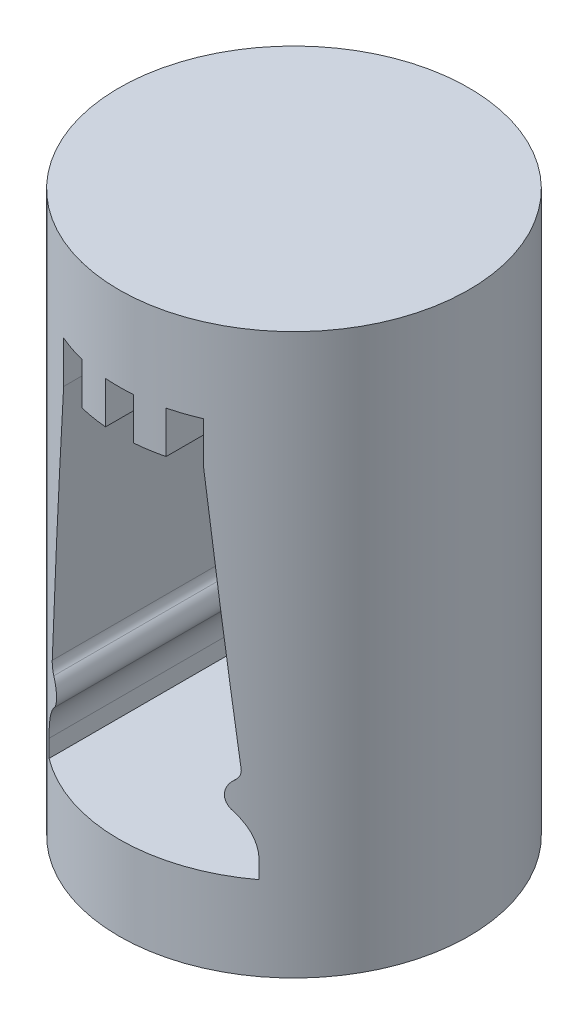
SolidWorks part; units mm, degrees
ref_plane "Front" through (0, 0, 0) normal (0, 0, 1) x (1, 0, 0)
ref_plane "Top" through (0, 0, 0) normal (0, 1, 0) x (1, 0, 0)
ref_plane "Right" through (0, 0, 0) normal (1, 0, 0) x (0, 0, -1)
sketch "Sketch2" plane through (0, 0, 0) normal (0, 1, 0) x (1, 0, 0)
  circle A0 centre (0, 0) radius 12.5
  dimension "D1" = 25
extrude "Boss-Extrude1" add sketch "Sketch2" along normal mid plane 40
sketch "Sketch3" plane through (0, 0, 0) normal (0, 0, 1) x (1, 0, 0)
  line L0 (-7.5, -14) -> (7.5, -14)
  line L2 (-7.5, -12.75) -> (-7.5, -14)
  line L3 (0, -50) -> (0, 50) construction
  line L5 (-5, 11) -> (-5, 14)
  line L6 (-5, 14) -> (-3, 14)
  line L7 (-3, 14) -> (-3, 11)
  line L8 (-3, 11) -> (-1, 11)
  line L9 (-1, 11) -> (-1, 14)
  line L17 (1, 11) -> (1, 14)
  line L18 (3, 11) -> (1, 11)
  line L19 (3, 14) -> (3, 11)
  line L20 (5, 14) -> (3, 14)
  line L21 (5, 11) -> (5, 14)
  line L23 (7.5, -12.75) -> (7.5, -14)
  line L24 (-1, 14) -> (1, 14)
  line L25 (-6.7499, -7.2906) -> (-5, 11)
  line L26 (6.7499, -7.2906) -> (5, 11)
  arc A4 (-6.3554, -9.8931) -> (-7.5, -12.75) centre (-3.3622, -12.75) ccw
  arc A6 (-6.456, -8.0123) -> (-6.3554, -9.8931) centre (-7.2911, -9) cw
  arc A13 (6.456, -8.0123) -> (6.3554, -9.8931) centre (7.2911, -9) ccw
  arc A14 (6.3554, -9.8931) -> (7.5, -12.75) centre (3.3622, -12.75) cw
  arc A15 (-6.456, -8.0123) -> (-6.7499, -7.2906) centre (-5.9135, -7.3706) cw
  arc A17 (6.456, -8.0123) -> (6.7499, -7.2906) centre (5.9135, -7.3706) ccw
  point P0 (0, -14)
  dimension "D1" = 14
  dimension "D6" = 1.25
  dimension "D7" = 5
  dimension "D2" = 15
  dimension "D3" = 14
  dimension "D4" = 3
  dimension "D5" = 2
extrude "Cut-Extrude1" cut sketch "Sketch3" against normal through all both and the other way through all
sketch "Sketch4" plane through (0, -20, 0) normal (0, -1, 0) x (-1, 0, 0)
  circle A0 centre (0, 0) radius 3
  dimension "D1" = 6
extrude "Cut-Extrude2" cut sketch "Sketch4" against normal blind 3
